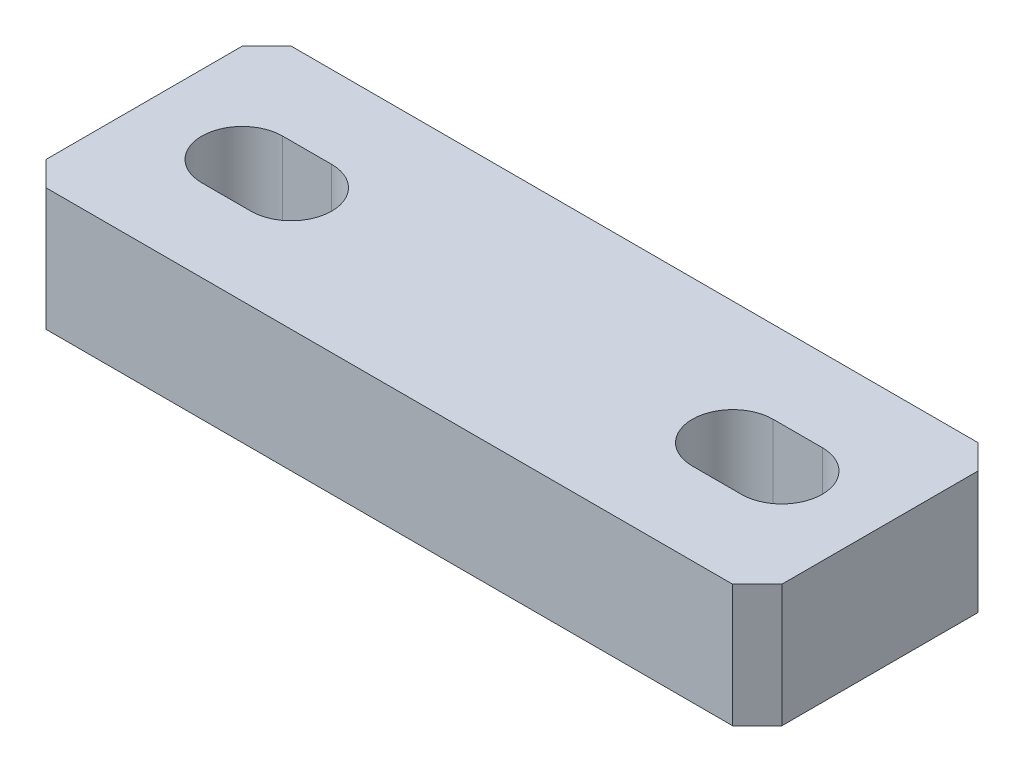
SolidWorks part; units mm, degrees
material "Lega 1060"
ref_plane "Piano frontale" through (0, 0, 0) normal (0, 0, 1) x (1, 0, 0)
ref_plane "Piano superiore" through (0, 0, 0) normal (0, 1, 0) x (1, 0, 0)
ref_plane "Piano destro" through (0, 0, 0) normal (1, 0, 0) x (0, 0, -1)
sketch "Schizzo1" plane through (0, 0, 0) normal (0, 0, 1) x (1, 0, 0)
  line L4 (-15, 0) -> (15, 0)
  line L5 (0, -4.2112) -> (0, 9.1781) construction
  line L7 (15, 0) -> (15, 5)
  line L8 (15, 5) -> (-15, 5)
  line L9 (-15, 5) -> (-15, 0)
  dimension "D1" = 5
  dimension "D4" = 30
extrude "Estrusione-Estrusione1" add sketch "Schizzo1" along normal blind 10
sketch "Schizzo2" plane through (0, 5, 0) normal (0, 1, 0) x (1, 0, 0)
  line L0 (-12.7999, -5) -> (12.1785, -5) construction
  line L1 (15, -10) -> (-15, -10) construction
  line L2 (15, 0) -> (-15, 0) construction
  line L5 (-11, -5) -> (-9, -5) construction
  line L6 (-11, -3.35) -> (-9, -3.35)
  line L7 (-11, -6.65) -> (-9, -6.65)
  line L8 (-15, -10) -> (-15, 0) construction
  line L9 (0, -10) -> (0, 0) construction
  line L10 (11, -5) -> (9, -5) construction
  line L11 (11, -3.35) -> (9, -3.35)
  line L12 (11, -6.65) -> (9, -6.65)
  arc A0 (-11, -3.35) -> (-11, -6.65) centre (-11, -5) ccw
  arc A1 (-9, -6.65) -> (-9, -3.35) centre (-9, -5) ccw
  arc A2 (11, -3.35) -> (11, -6.65) centre (11, -5) cw
  arc A3 (9, -6.65) -> (9, -3.35) centre (9, -5) cw
  point P8 (-10, -5)
  point P19 (10, -5)
  dimension "D1" = 3.3
  dimension "D2" = 5
  dimension "D3" = 2
extrude "Taglio-Estrusione1" cut sketch "Schizzo2" against normal blind 10
chamfer "Smusso1" distance 1 angle 45 1 edges at (-15, 2.5, 10)
chamfer "Smusso2" distance 1 angle 45 3 edges at (15, 2.5, 10) (15, 2.5, 0) (-15, 2.5, 0)
